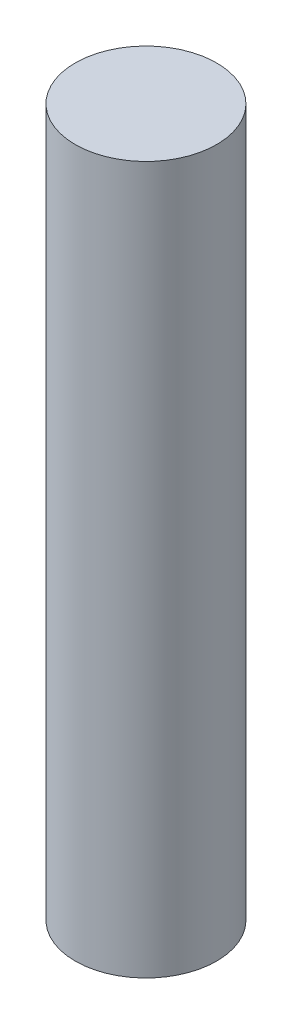
SolidWorks part; units mm, degrees
ref_plane "Front" through (0, 0, 0) normal (0, 0, 1) x (1, 0, 0)
ref_plane "Top" through (0, 0, 0) normal (0, 1, 0) x (1, 0, 0)
ref_plane "Right" through (0, 0, 0) normal (1, 0, 0) x (0, 0, -1)
sketch "Sketch1" plane through (0, 0, 0) normal (0, 1, 0) x (1, 0, 0)
  circle A0 centre (0, 0) radius 5
  dimension "D1" = 10
extrude "Boss-Extrude1" add sketch "Sketch1" along normal blind 50
sketch "Sketch2" plane through (0, 0, 0) normal (0, 0, 1) x (1, 0, 0)
  line L0 (0, 0) -> (0, 50) construction
  line L1 (5, 50) -> (-5, 50) construction
  point P6 (0, 25)
